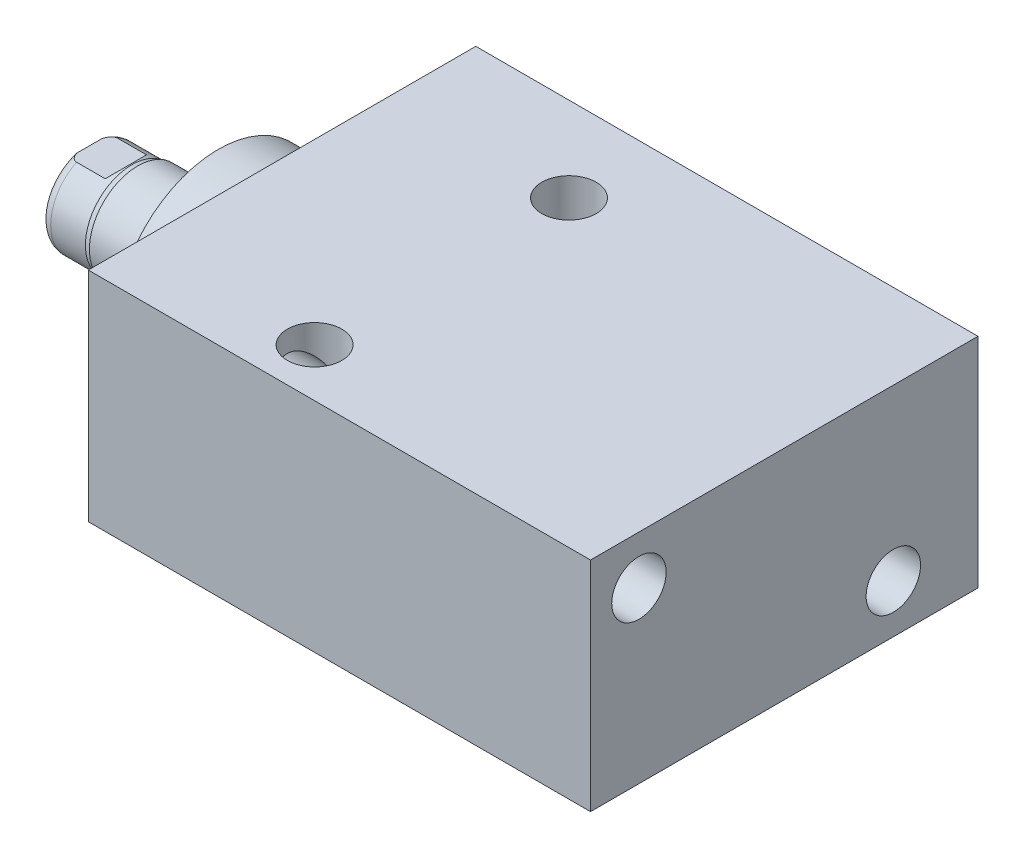
SolidWorks part; units mm, degrees
material "Alloy Steel"
ref_plane "Front Plane" through (0, 0, 0) normal (0, 0, 1) x (1, 0, 0)
ref_plane "Top Plane" through (0, 0, 0) normal (0, 1, 0) x (1, 0, 0)
ref_plane "Right Plane" through (0, 0, 0) normal (1, 0, 0) x (0, 0, -1)
ref_plane "Plane1" through (0, 0, 0) normal (1, 0, 0) x (0, 0, -1)
sketch "Sketch1" plane through (0, 0, 0) normal (1, 0, 0) x (0, 0, -1)
  line L0 (-23.0124, 14.2875) -> (27.7876, 14.2875)
  line L1 (27.7876, 14.2875) -> (27.7876, -14.2875)
  line L2 (27.7876, -14.2875) -> (-23.0124, -14.2875)
  line L3 (-23.0124, -14.2875) -> (-23.0124, 14.2875)
  line L4 (0, -24.4475) -> (0, 24.4475) construction
  dimension "D1" = 28.575
  dimension "D2" = 14.2875
  dimension "D3" = 50.8
  dimension "D4" = 23.0124
extrude "Extrude1" add sketch "Sketch1" along normal blind 65.8368
ref_plane "Plane12" through (0, 4.7625, 0) normal (0, 1, 0) x (-1, 0, 0)
sketch "S2D0002" plane through (0, 4.7625, 0) normal (0, 1, 0) x (-1, 0, 0)
  line L0 (-14.5415, -27.5336) -> (-18.161, -27.5336)
  line L1 (-14.5415, -27.5082) -> (-14.5415, -27.5336)
  line L2 (-14.5415, -27.5082) -> (-13.9446, -26.9113)
  line L3 (-13.9446, -26.9113) -> (-13.9446, -14.0716)
  line L4 (-13.9446, -14.0716) -> (-9.525, -14.0716)
  line L5 (-9.525, -14.0716) -> (-9.525, -27.7876)
  line L6 (-9.525, -19.1384) -> (-9.525, 0.6985) construction
  line L7 (0, -27.7876) -> (0, 23.0124) construction
  line L8 (-18.161, -27.7876) -> (-18.161, -27.5336)
  line L9 (-65.8368, -27.7876) -> (0, -27.7876) construction
  line L10 (-18.161, -27.7876) -> (-9.525, -27.7876)
  dimension "D1" = 13.716
  dimension "D2" = 9.525
  dimension "D3" = 8.8392
  dimension "D4" = 45
  dimension "D5" = 0.6223
  dimension "D6" = 10.033
  dimension "D7" = 0.0254
  dimension "D8" = 0.254
  dimension "D9" = 17.272
revolve "Cut-Revolve1" cut sketch "S2D0002" angle 360 about L6
pattern_linear "LPattern1" count 2 spacing 46.99 along (1, 0, 0) of "Cut-Revolve1"
sketch "Sketch5" plane through (0, 0, 0) normal (-1, 0, 0) x (0, 0, 1)
  circle A0 centre (0, 0) radius 13.5001
  dimension "D1" = 27.0002
extrude "Extrude2" add sketch "Sketch5" along normal blind 5.969
ref_plane "Plane5" through (0, 0, 0) normal (0, -1, 0) x (0, 0, 1)
sketch "Sketch6" plane through (0, 0, 0) normal (0, -1, 0) x (0, 0, 1)
  line L0 (0, 5.969) -> (-6.3373, 5.969)
  line L1 (-6.3373, 5.969) -> (-6.3373, 22.86)
  line L2 (-6.3373, 22.86) -> (0, 22.86)
  line L3 (0, 22.86) -> (0, 5.969)
  line L4 (0, -5.7546) -> (0, 21.1709) construction
  line L5 (13.5001, 5.969) -> (-13.5001, 5.969) construction
  line L6 (23.0124, -65.8368) -> (-27.7876, -65.8368) construction
  dimension "D1" = 88.6968
  dimension "D2" = 12.6746
revolve "Revolve1" add sketch "Sketch6" angle 360 about L4
ref_plane "Plane6" through (-18.5113, 3.2639, 0) normal (0, 0, 1) x (0, 1, 0)
sketch "S2D0001" plane through (-18.5113, 3.2639, 0) normal (0, 0, 1) x (0, 1, 0)
  line L0 (-0.7493, 2.9849) -> (-0.7493, -11.6533)
  line L1 (-3.2639, -13.1642) -> (-0.7493, -11.6533)
  line L2 (0.0381, 4.3487) -> (-3.2639, 4.3487)
  line L3 (-3.2639, 4.3487) -> (-3.2639, -13.1642)
  line L4 (-0.7493, 2.9849) -> (0.0381, 4.3487)
  line L5 (-3.2639, -18.5113) -> (-3.2639, 2.765) construction
  line L6 (3.0734, 4.3487) -> (-9.6012, 4.3487) construction
  dimension "D1" = 30
  dimension "D2" = 6.604
  dimension "D3" = 5.0292
  dimension "D4" = 16.002
  dimension "D5" = 59
revolve "Cut-Revolve4" cut sketch "S2D0001" angle 360 about L5
ref_plane "Plane7" through (0, 0, 0) normal (0, 1, 0) x (0, 0, -1)
sketch "Sketch8" plane through (0, 0, 0) normal (0, 1, 0) x (0, 0, -1)
  line L0 (-6.3373, 16.5354) -> (-6.096, 17.2974)
  line L1 (-6.096, 17.2974) -> (-6.096, 21.844)
  line L2 (0, 12.6594) -> (0, 20.8178) construction
  line L3 (-6.3373, 16.5354) -> (-6.3373, 22.86)
  line L4 (-5.7079, 22.86) -> (-6.3373, 22.86)
  line L5 (6.3373, 22.86) -> (-6.3373, 22.86) construction
  line L6 (-6.3373, 22.86) -> (-6.3373, 5.969) construction
  arc A0 (-5.7079, 22.86) -> (-6.096, 21.844) centre (-4.572, 21.844) ccw
  dimension "D2" = 1.524
  dimension "D1" = 12.192
  dimension "D3" = 1.016
  dimension "D4" = 0.762
  dimension "D5" = 5.5626
revolve "Cut-Revolve5" cut sketch "Sketch8" angle 360 about L2
ref_plane "Plane11" through (0, 0, 0) normal (0, 0, -1) x (0, -1, 0)
sketch "Sketch12" plane through (0, 0, 0) normal (0, 0, -1) x (0, -1, 0)
  line L0 (5.461, 22.86) -> (5.461, 18.0848)
  line L1 (5.461, 18.0848) -> (6.096, 17.4498)
  line L2 (-5.461, 22.86) -> (-5.461, 18.0848)
  line L3 (-5.461, 18.0848) -> (-6.096, 17.4498)
  line L4 (5.461, 22.86) -> (6.096, 22.86)
  line L5 (0, 13.7262) -> (0, 20.767) construction
  line L6 (-6.096, 17.4498) -> (-6.096, 22.86)
  line L8 (6.096, 17.2974) -> (6.096, 21.844) construction
  line L9 (6.096, 17.4498) -> (6.096, 22.86)
  line L10 (-5.461, 22.86) -> (-6.096, 22.86)
  line L12 (5.7079, 22.86) -> (-5.7079, 22.86) construction
  dimension "D1" = 10.922
  dimension "D2" = 4.7752
  dimension "D3" = 45
extrude "Cut-Extrude4" cut sketch "Sketch12" against normal mid plane 60.96
hole_wizard "Hole1" positions "Sketch15" profile "Sketch14" legacy end condition up to next
sketch "Sketch15" plane through (0, 0, 0) normal (-1, 0, 0) x (0, 0, 1)
  line L0 (0, 0) -> (-29.9914, 0) construction
  line L1 (0, 0) -> (0, 25.7648) construction
  point P0 (-16.6878, -7.9248)
  point P11 (16.6624, 7.9502)
  dimension "D1" = 7.9248
  dimension "D2" = 16.6878
  dimension "D3" = 15.875
  dimension "D4" = 33.3502
sketch "Sketch14" plane through (0, -7.9248, -16.6878) normal (0, 1, 0) x (0, 0, 1)
  line L0 (0, 0) -> (0, 65.8368)
  line L1 (0, 65.8368) -> (3.5685, 65.8368)
  line L2 (3.5685, 65.8368) -> (3.5685, 0)
  line L3 (3.5685, 0) -> (0, 0)
  line L4 (0, 110) -> (0, -10) construction
  dimension "Diameter" = 7.137
  dimension "Depth" = 65.8368
hole_wizard "Hole2" positions "Sketch17" profile "Sketch16" legacy
sketch "Sketch17" plane through (0, 14.2875, 0) normal (0, 1, 0) x (-1, 0, 0)
  line L0 (0, 0) -> (-59.3363, 0) construction
  line L1 (0, -27.7876) -> (0, 23.0124) construction
  point P0 (-23.3172, -16.6878)
  point P9 (-23.3172, 16.6624)
  dimension "D1" = 33.3502
  dimension "D2" = 23.3172
  dimension "D3" = 16.6878
sketch "Sketch16" plane through (23.3172, 14.2875, -16.6878) normal (1, 0, 0) x (0, 0, 1)
  line L0 (0, 0) -> (0, 28.575)
  line L1 (0, 28.575) -> (3.5685, 28.575)
  line L2 (3.5685, 28.575) -> (3.5685, 0)
  line L3 (3.5685, 0) -> (0, 0)
  line L4 (0, 110) -> (0, -10) construction
  dimension "Diameter" = 7.137
  dimension "Depth" = 28.575
